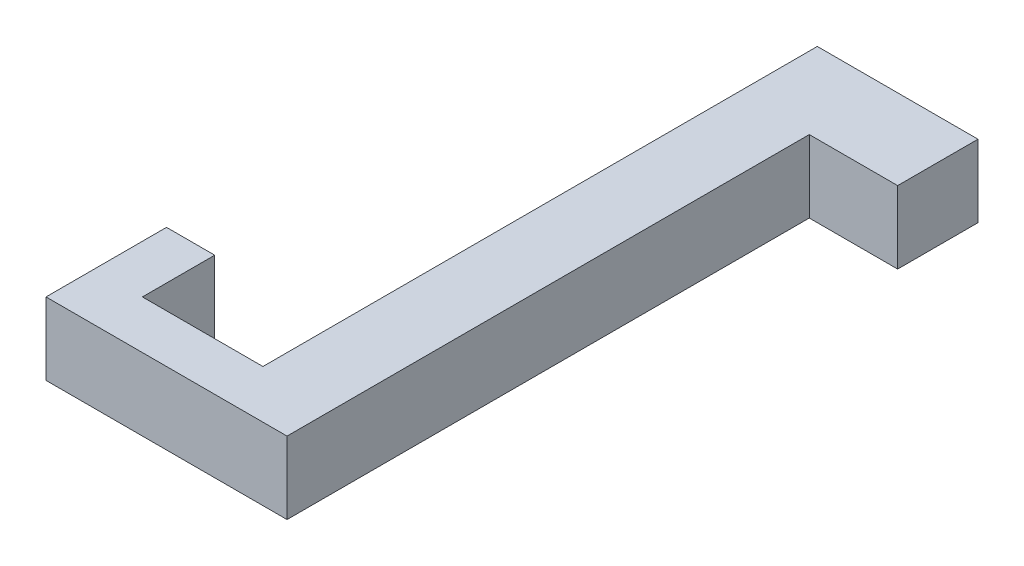
SolidWorks part; units mm, degrees
material "Teak"
ref_plane "Front Plane" through (0, 0, 0) normal (0, 0, 1) x (1, 0, 0)
ref_plane "Top Plane" through (0, 0, 0) normal (0, 1, 0) x (1, 0, 0)
ref_plane "Right Plane" through (0, 0, 0) normal (1, 0, 0) x (0, 0, -1)
sketch "Sketch1" plane through (0, 0, 0) normal (0, 1, 0) x (1, 0, 0)
  line L21 (0, -16.25) -> (0, 16.25) construction
  line L22 (0.5, 16.25) -> (5.5, 16.25) construction
  line L23 (5.5, 21.25) -> (-4.5, 21.25) construction
  line L24 (-4.5, 21.25) -> (-4.5, -8.75) construction
  line L25 (0, 16.25) -> (5.5, 16.25) construction
  line L26 (5.5, 16.25) -> (5.5, 21.25) construction
  line L27 (0, -16.25) -> (-15, -16.25) construction
  line L28 (-15, -16.25) -> (-15, -8.75) construction
  line L29 (-4.5, -13.25) -> (-4.5, -8.75) construction
  line L30 (-15, -8.75) -> (-12, -8.75) construction
  line L31 (-12, -8.75) -> (-12, -13.25) construction
  line L32 (-12, -13.25) -> (-4.5, -13.25) construction
sketch "Sketch2" plane through (0, 0, 0) normal (0, 1, 0) x (1, 0, 0)
  line L0 (0, -16.25) -> (-15, -16.25) construction
  line L1 (-15, -16.25) -> (-15, -8.75) construction
  line L2 (-15, -8.75) -> (-12, -8.75) construction
  line L3 (-12, -8.75) -> (-12, -13.25) construction
  line L4 (-12, -13.25) -> (-4.5, -13.25) construction
  line L5 (5.5, 16.25) -> (5.5, 21.25) construction
  line L6 (5.5, 21.25) -> (-4.5, 21.25) construction
  line L7 (0, -16.25) -> (0, 16.25) construction
  line L8 (0, -16.25) -> (-15, -16.25)
  line L9 (-15, -16.25) -> (-15, -8.75)
  line L10 (-15, -8.75) -> (-12, -8.75)
  line L11 (-12, -8.75) -> (-12, -13.25)
  line L12 (-12, -13.25) -> (-4.5, -13.25)
  line L13 (5.5, 16.25) -> (5.5, 21.25)
  line L14 (5.5, 21.25) -> (-4.5, 21.25)
  line L15 (0, -16.25) -> (0, 16.25)
  line L16 (-4.5, -13.25) -> (-4.5, 21.25)
  line L17 (0, 16.25) -> (5.5, 16.25)
extrude "Boss-Extrude1" add sketch "Sketch2" along normal blind 4.5
